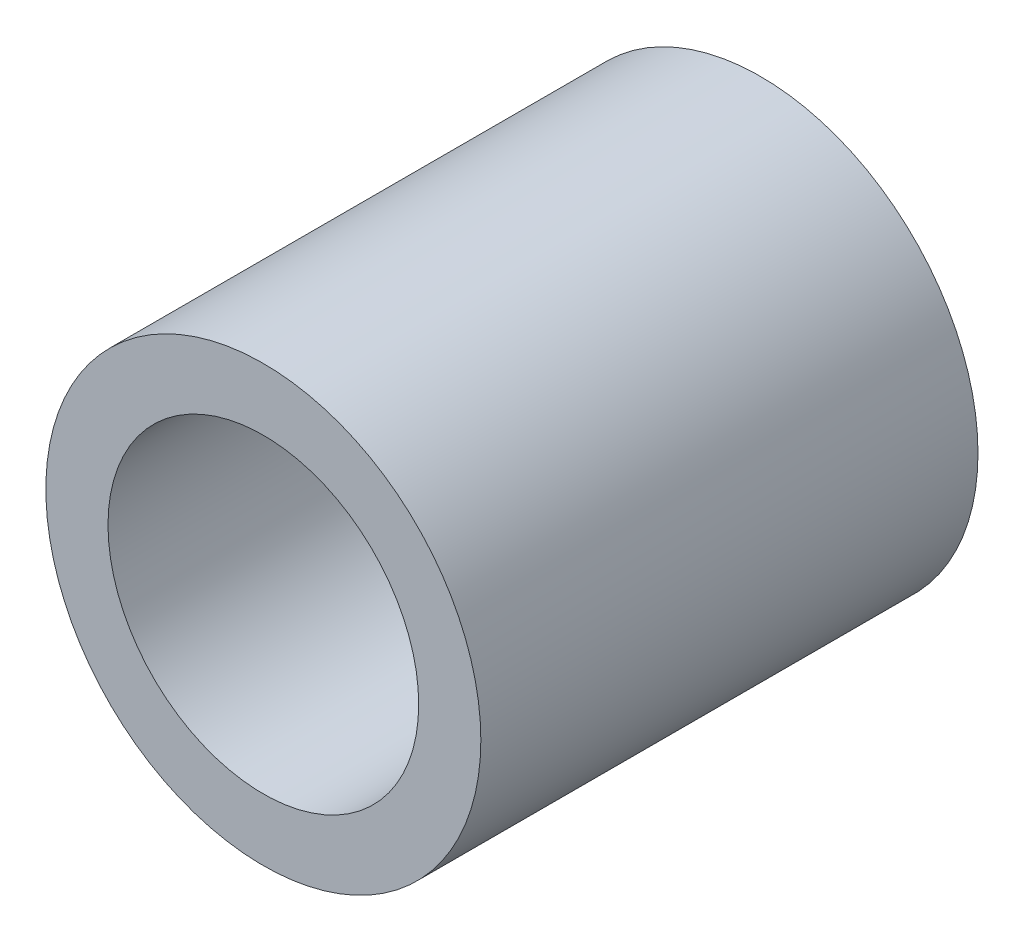
SolidWorks part; units mm, degrees
ref_plane "Front Plane" through (0, 0, 0) normal (0, 0, 1) x (1, 0, 0)
ref_plane "Top Plane" through (0, 0, 0) normal (0, 1, 0) x (1, 0, 0)
ref_plane "Right Plane" through (0, 0, 0) normal (1, 0, 0) x (0, 0, -1)
sketch "Sketch1" plane through (0, 0, 0) normal (0, 0, 1) x (1, 0, 0)
  circle A0 centre (0, 0) radius 6.25
  dimension "D1" = 12.5
extrude "Extrude-Thin1" add sketch "Sketch1" along normal blind 20 thin
